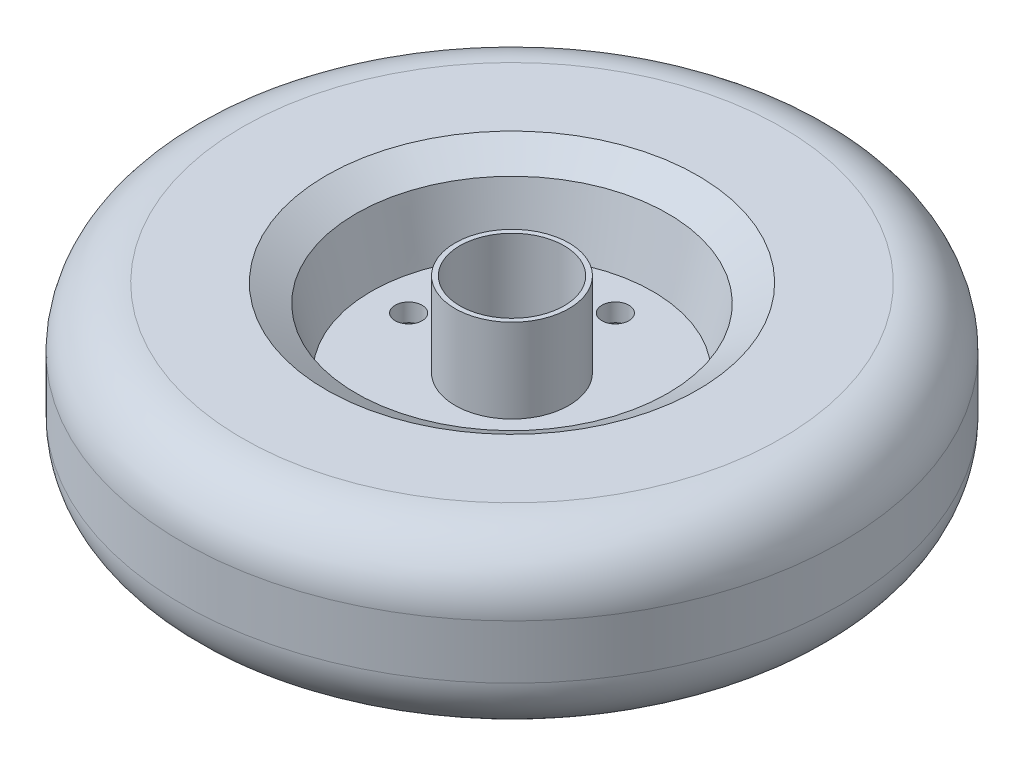
SolidWorks part; units mm, degrees
ref_plane "Alzado" through (0, 0, 0) normal (0, 0, 1) x (1, 0, 0)
ref_plane "Planta" through (0, 0, 0) normal (0, 1, 0) x (1, 0, 0)
ref_plane "Vista lateral" through (0, 0, 0) normal (1, 0, 0) x (0, 0, -1)
sketch "Croquis2" plane through (0, 0, 0) normal (0, 0, 1) x (1, 0, 0)
  line L0 (0, 31) -> (19, 31)
  line L1 (19, 31) -> (19, 3)
  line L2 (19, 3) -> (47, 3)
  line L3 (47, 3) -> (52, 23)
  line L4 (52, 23) -> (62, 29)
  line L5 (62, 29) -> (90, 29)
  line L6 (110, 9) -> (110, -9)
  line L7 (110, 0) -> (0, 0)
  line L8 (0, -31) -> (0, 31)
  line L9 (0, 64.7683) -> (0, -22.9111) construction
  line L10 (-41.779, 0) -> (154.4253, 0) construction
  line L11 (62, -29) -> (90, -29)
  line L12 (52, -23) -> (62, -29)
  line L13 (47, -3) -> (52, -23)
  line L14 (19, -3) -> (47, -3)
  line L15 (19, -31) -> (19, -3)
  line L16 (0, -31) -> (19, -31)
  arc A0 (90, 29) -> (110, 9) centre (90, 9) cw
  arc A1 (90, -29) -> (110, -9) centre (90, -9) ccw
  point P11 (110, 29)
  point P26 (110, -29)
  dimension "D10" = 20
  dimension "D1" = 19
  dimension "D2" = 28
  dimension "D3" = 48
  dimension "D4" = 10
  dimension "D5" = 5
  dimension "D6" = 29
  dimension "D7" = 28
  dimension "D8" = 3
  dimension "D9" = 20
revolve "Revolución1" add sketch "Croquis2" angle 360 about L9
hole_wizard "Taladro de margen para M101" positions "Croquis3" profile "Croquis4" hole size "M10" standard "ISO" end condition through all
sketch "Croquis3" plane through (0, 31, 0) normal (0, 1, 0) x (1, 0, 0)
  point P0 (0, 0)
sketch "Croquis4" plane through (0, 31, 0) normal (1, 0, 0) x (0, 0, 1)
  line L0 (0, 0) -> (0, 62)
  line L1 (0, 62) -> (5.5, 62)
  line L2 (5.5, 62) -> (5.5, 0)
  line L5 (5.5, 0) -> (0, 0)
  line L11 (0, -6.35) -> (0, 107.95) construction
  dimension "Diámetro de taladro hasta el siguiente" = 11
  dimension "Profundidad de taladro hasta el siguiente" = 62
hole_wizard "Taladro de margen para M81" positions "Croquis5" profile "Croquis6" hole size "M8" standard "ISO" end condition through all
sketch "Croquis5" plane through (0, 3, 0) normal (0, 1, 0) x (1, 0, 0)
  point P0 (0, 34.5)
  dimension "D1" = 34.5
sketch "Croquis6" plane through (0, 3, -34.5) normal (1, 0, 0) x (0, 0, 1)
  line L0 (0, 0) -> (0, 34)
  line L1 (0, 34) -> (4.5, 34)
  line L2 (4.5, 34) -> (4.5, 0)
  line L5 (4.5, 0) -> (0, 0)
  line L11 (0, -6.35) -> (0, 107.95) construction
  dimension "Diámetro de taladro hasta el siguiente" = 9
  dimension "Profundidad de taladro hasta el siguiente" = 34
pattern_circular "MatrizC1" count 4 over 360 about axis through (0, 0, 0) along (0, 1, 0) of "Taladro de margen para M81"
sketch "Croquis8" plane through (0, 31, 0) normal (0, 1, 0) x (1, 0, 0)
  circle A0 centre (0, 0) radius 17.4
  circle A1 centre (0, 0) radius 19
  circle A2 centre (0, 0) radius 19
  dimension "D1" = 0
  dimension "D2" = 1.6
extrude "Cortar-Extruir2" cut sketch "Croquis8" against normal blind 70 contours A0
